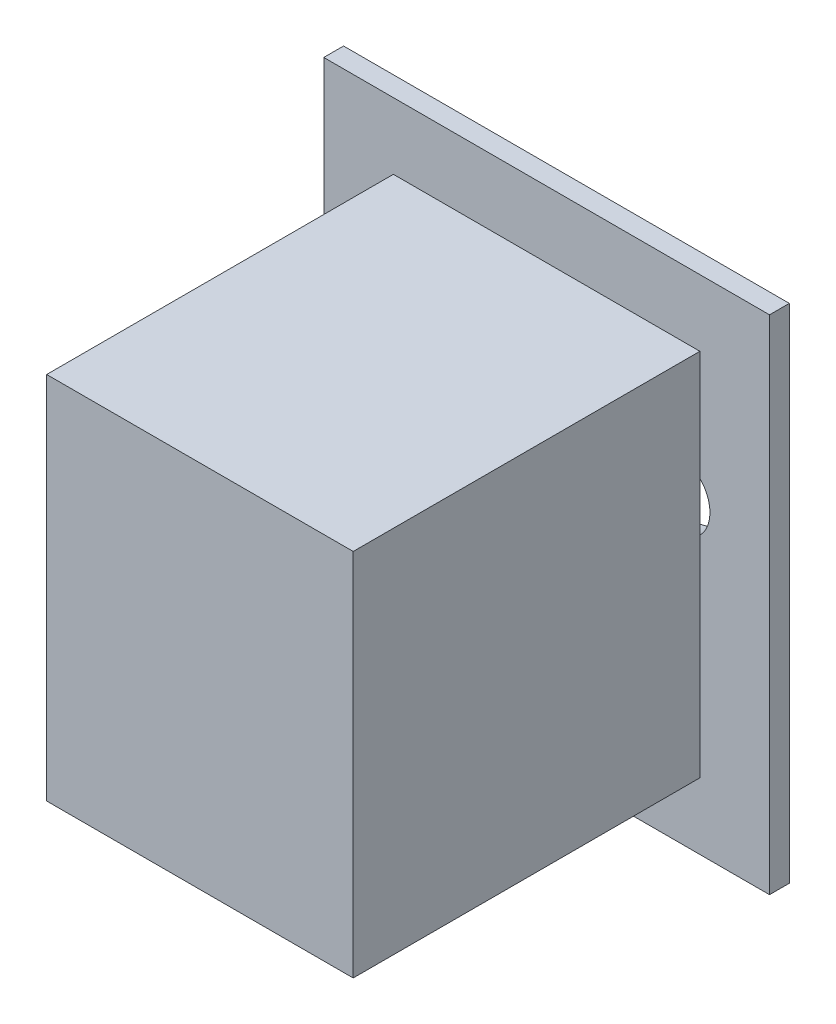
SolidWorks part; units mm, degrees
ref_plane "Front Plane" through (0, 0, 0) normal (0, 0, 1) x (1, 0, 0)
ref_plane "Top Plane" through (0, 0, 0) normal (0, 1, 0) x (1, 0, 0)
ref_plane "Right Plane" through (0, 0, 0) normal (1, 0, 0) x (0, 0, -1)
sketch "Sketch1" plane through (0, 0, 0) normal (0, 0, 1) x (1, 0, 0)
  line L0 (0, 0) -> (0, 15.6212) construction
  line L1 (-22.5, -25.35) -> (22.5, -25.35)
  line L2 (-22.5, -25.35) -> (-22.5, 25.35)
  line L3 (-22.5, 25.35) -> (22.5, 25.35)
  line L4 (22.5, -25.35) -> (22.5, 25.35)
  line L5 (-22.5, -25.35) -> (22.5, 25.35) construction
  line L6 (-22.5, 25.35) -> (22.5, -25.35) construction
  circle A0 centre (0, 15.6212) radius 2.637
  circle A1 centre (-12.9329, 5.051) radius 3.5541
  circle A2 centre (-9.0475, -11.6008) radius 2.9891
  circle A3 centre (9.0475, -11.6008) radius 2.9891
  circle A4 centre (12.9329, 5.051) radius 3.5541
  point P0 (0, 0)
  dimension "D1" = 50.7
  dimension "D2" = 45
extrude "Boss-Extrude1" add sketch "Sketch1" along normal blind 2
sketch "Sketch2" plane through (0, 0, 2) normal (0, 0, 1) x (1, 0, 0)
  line L1 (-15.4718, -18.646) -> (15.4718, -18.646)
  line L2 (-15.4718, -18.646) -> (-15.4718, 18.646)
  line L3 (-15.4718, 18.646) -> (15.4718, 18.646)
  line L4 (15.4718, -18.646) -> (15.4718, 18.646)
  line L5 (-15.4718, -18.646) -> (15.4718, 18.646) construction
  line L6 (-15.4718, 18.646) -> (15.4718, -18.646) construction
  point P0 (0, 0)
extrude "Boss-Extrude2" add sketch "Sketch2" along normal blind 35
